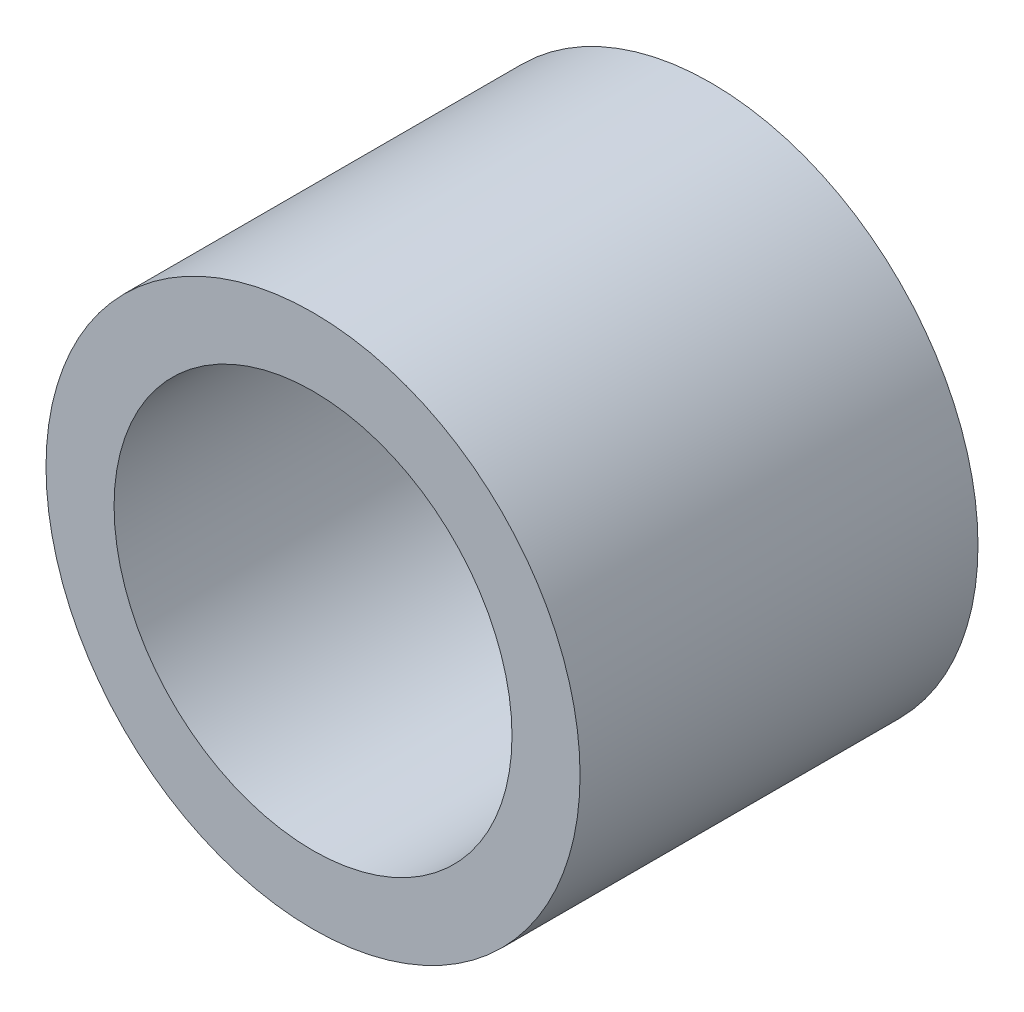
SolidWorks part; units mm, degrees
ref_plane "Front Plane" through (0, 0, 0) normal (0, 0, 1) x (1, 0, 0)
ref_plane "Top Plane" through (0, 0, 0) normal (0, 1, 0) x (1, 0, 0)
ref_plane "Right Plane" through (0, 0, 0) normal (1, 0, 0) x (0, 0, -1)
sketch "Sketch1" plane through (0, 0, 0) normal (0, 0, 1) x (1, 0, 0)
  circle A0 centre (0, 0) radius 12.75
  circle A1 centre (0, 0) radius 9.5
  dimension "D1" = 25.5
  dimension "D2" = 19
extrude "Boss-Extrude1" add sketch "Sketch1" along normal blind 19
